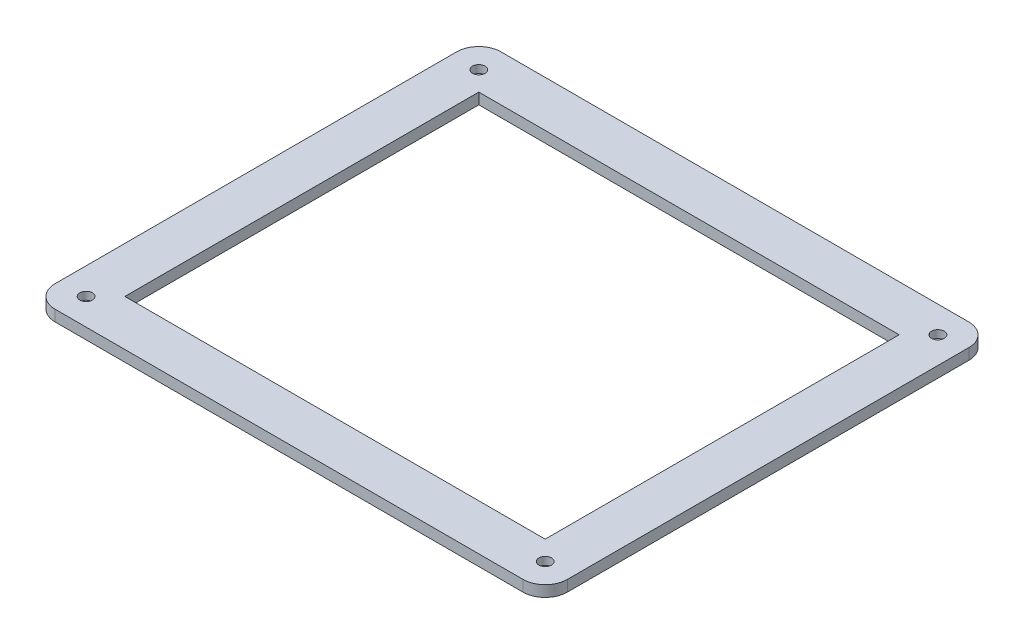
SolidWorks part; units mm, degrees
ref_plane "Front Plane" through (0, 0, 0) normal (0, 0, 1) x (1, 0, 0)
ref_plane "Top Plane" through (0, 0, 0) normal (0, 1, 0) x (1, 0, 0)
ref_plane "Right Plane" through (0, 0, 0) normal (1, 0, 0) x (0, 0, -1)
sketch "Sketch1" plane through (0, 0, 0) normal (0, 1, 0) x (1, 0, 0)
  line L1 (-94.95, 79.95) -> (94.95, 79.95)
  line L2 (-94.95, 79.95) -> (-94.95, -79.95)
  line L3 (-94.95, -79.95) -> (94.95, -79.95)
  line L4 (94.95, 79.95) -> (94.95, -79.95)
  line L5 (-115.7, 100.7) -> (115.7, 100.7)
  line L6 (-115.7, 100.7) -> (-115.7, -100.7)
  line L7 (-115.7, -100.7) -> (115.7, -100.7)
  line L8 (115.7, 100.7) -> (115.7, -100.7)
  point P4 (-94.95, 0)
  point P6 (0, 79.95)
  point P11 (0, -100.7)
  point P12 (-115.7, 0)
  dimension "D1" = 189.9
  dimension "D2" = 159.9
  dimension "D3" = 20.75
  dimension "D4" = 20.75
extrude "Boss-Extrude1" add sketch "Sketch1" along normal blind 5
fillet "Fillet1" radius 10 4 edges at (-115.7, 2.5, -100.7) (115.7, 2.5, -100.7) (115.7, 2.5, 100.7) (-115.7, 2.5, 100.7)
sketch "Sketch2" plane through (0, 0, 0) normal (0, -1, 0) x (1, 0, 0)
  line L0 (-105.7, 100.7) -> (105.7, 100.7) construction
  line L1 (-115.7, -90.7) -> (-115.7, 90.7) construction
  circle A0 centre (-103.7, 88.7) radius 5.85
  dimension "D3" = 11.7
  dimension "D1" = 12
  dimension "D2" = 12
extrude "Boss-Extrude2" add sketch "Sketch2" along normal blind 2.5
sketch "Sketch3" plane through (0, 5, 0) normal (0, 1, 0) x (1, 0, 0)
  line L2 (-115.7, 90.7) -> (-115.7, -90.7) construction
  line L3 (-105.7, -100.7) -> (105.7, -100.7) construction
  circle A0 centre (-103.7, -88.7) radius 1.55
  dimension "D1" = 3.1
  dimension "D2" = 12
  dimension "D3" = 12
extrude "Cut-Extrude1" cut sketch "Sketch3" against normal blind 7.5
sketch "Sketch4" plane through (0, 5, 0) normal (0, 1, 0) x (1, 0, 0)
  circle A0 centre (-103.7, -88.7) radius 2.85
  dimension "D1" = 5.7
extrude "Cut-Extrude2" cut sketch "Sketch4" against normal blind 3.5
mirror "Mirror3" about plane through (0, 0, 0) normal (1, 0, 0) of "Cut-Extrude1", "Cut-Extrude2", "Boss-Extrude2"
mirror "Mirror4" about plane through (0, 0, 0) normal (0, 0, 1) of "Mirror3", "Boss-Extrude2", "Cut-Extrude1", "Cut-Extrude2"
